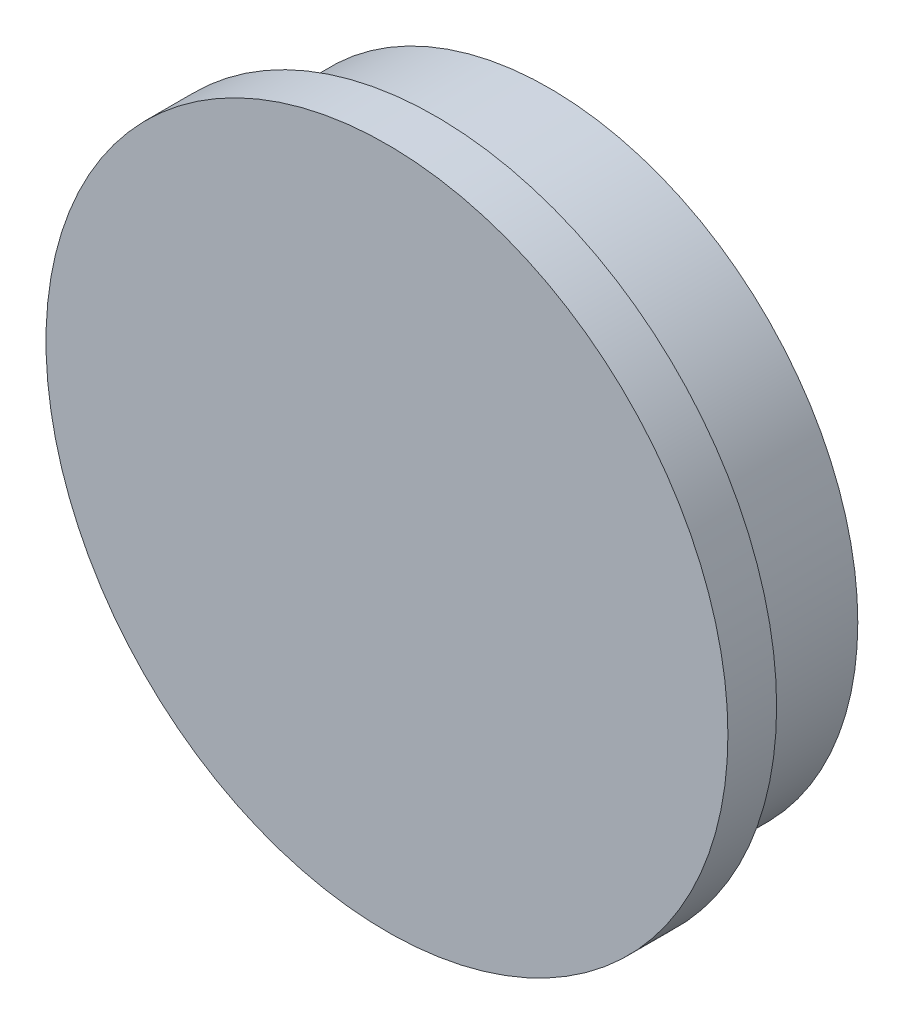
SolidWorks part; units mm, degrees
ref_plane "Спереди" through (0, 0, 0) normal (0, 0, 1) x (1, 0, 0)
ref_plane "Сверху" through (0, 0, 0) normal (0, 1, 0) x (1, 0, 0)
ref_plane "Справа" through (0, 0, 0) normal (1, 0, 0) x (0, 0, -1)
sketch "Эскиз2" plane through (0, 0, 0) normal (1, 0, 0) x (0, 0, -1)
  line L0 (0, 0) -> (0, 21)
  line L1 (0, 21) -> (3, 21)
  line L2 (3, 21) -> (3, 19)
  line L3 (3, 19) -> (10, 19)
  line L4 (0, 0) -> (10, 0)
  line L5 (10, 19) -> (10, 0)
  dimension "D1" = 21
  dimension "D2" = 7
  dimension "D3" = 19
  dimension "D4" = 3
revolve "Повернуть1" add sketch "Эскиз2" angle 360 about L4
sketch "Эскиз5" plane through (0, 0, 0) normal (0, 0, 1) x (1, 0, 0)
  line L1 (0, 0) -> (19, 0) construction
  circle A1 centre (0, 0) radius 19 construction
  circle A3 centre (0, 0) radius 19 construction
